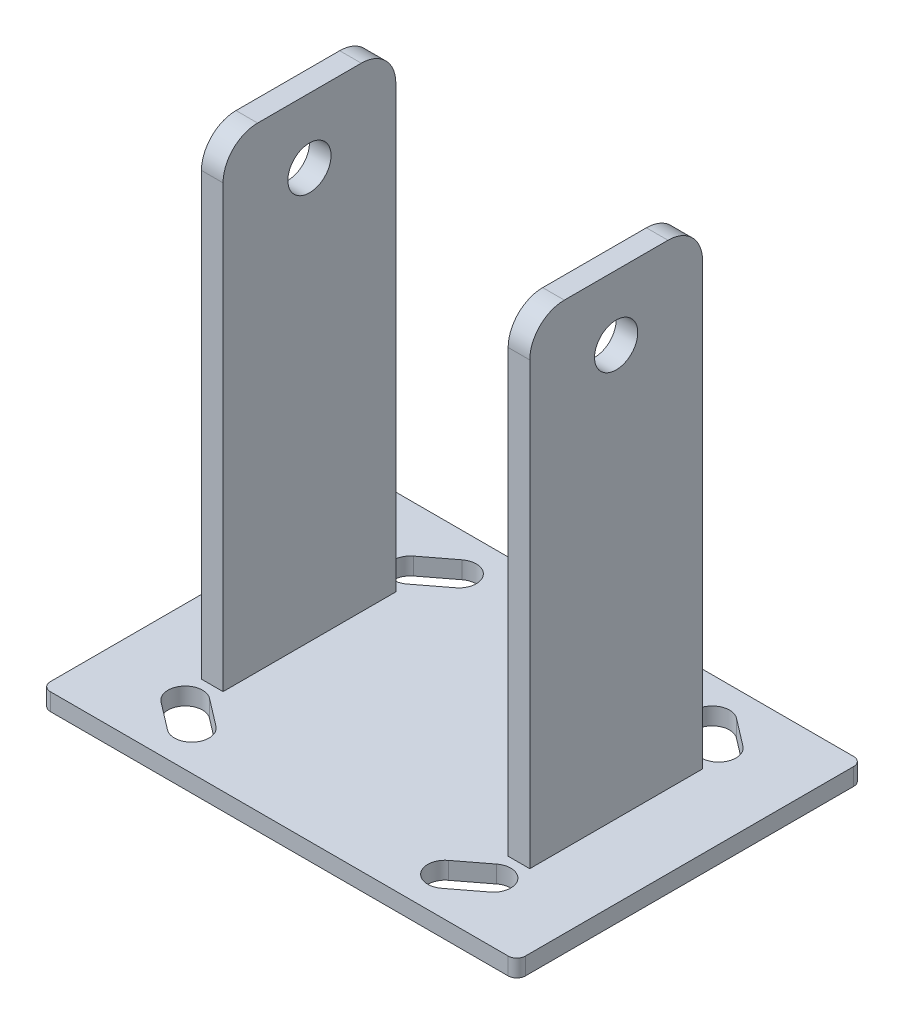
SolidWorks part; units mm, degrees
ref_plane "Front Plane" through (0, 0, 0) normal (0, 0, 1) x (1, 0, 0)
ref_plane "Top Plane" through (0, 0, 0) normal (0, 1, 0) x (1, 0, 0)
ref_plane "Right Plane" through (0, 0, 0) normal (1, 0, 0) x (0, 0, -1)
sketch "Sketch1" plane through (0, 0, 0) normal (0, 1, 0) x (1, 0, 0)
  line L0 (-69.85, 0) -> (69.85, 0) construction
  line L1 (69.85, 50.8) -> (-69.85, 50.8)
  line L2 (69.85, 50.8) -> (69.85, -50.8)
  line L3 (69.85, -50.8) -> (-69.85, -50.8)
  line L4 (-69.85, 50.8) -> (-69.85, -50.8)
  line L5 (69.85, 50.8) -> (-69.85, -50.8) construction
  line L6 (69.85, -50.8) -> (-69.85, 50.8) construction
  line L7 (0, 50.8) -> (0, -50.8) construction
  line L8 (-52.07, 50.8) -> (-52.07, -50.8) construction
  line L9 (52.07, 50.8) -> (52.07, -50.8) construction
  line L10 (-30.48, 50.8) -> (-30.48, -50.8) construction
  line L11 (30.48, 50.8) -> (30.48, -50.8) construction
  line L12 (-69.85, 27.94) -> (69.85, 27.94) construction
  line L13 (-69.85, 44.45) -> (69.85, 44.45) construction
  line L14 (-52.07, 27.94) -> (-30.48, 44.45) construction
  line L15 (-52.07, 44.45) -> (-30.48, 27.94) construction
  line L16 (-33.2043, 42.3667) -> (-49.3457, 30.0233) construction
  line L17 (-46.2598, 25.988) -> (-30.1185, 38.3314) construction
  line L18 (-46.2598, 25.988) -> (-52.4315, 34.0586) construction
  line L19 (-30.1185, 38.3314) -> (-36.2902, 46.402) construction
  line L20 (-52.4315, 34.0586) -> (-36.2902, 46.402) construction
  line L21 (-46.2598, 25.988) -> (-36.2902, 46.402) construction
  line L22 (-30.1185, 38.3314) -> (-52.4315, 34.0586) construction
  line L23 (-40.3255, 43.3162) -> (-34.1538, 35.2455) construction
  line L24 (-48.3962, 37.1445) -> (-42.2245, 29.0738) construction
  line L25 (-48.3962, 37.1445) -> (-40.3255, 43.3162)
  line L26 (-34.1538, 35.2455) -> (-42.2245, 29.0738)
  line L27 (34.1538, 35.2455) -> (42.2245, 29.0738)
  line L28 (48.3962, 37.1445) -> (40.3255, 43.3162)
  line L29 (34.1538, -35.2455) -> (42.2245, -29.0738)
  line L30 (48.3962, -37.1445) -> (40.3255, -43.3162)
  line L31 (-48.3962, -37.1445) -> (-40.3255, -43.3162)
  line L32 (-34.1538, -35.2455) -> (-42.2245, -29.0738)
  arc A0 (-40.3255, 43.3162) -> (-34.1538, 35.2455) centre (-37.2397, 39.2808) cw
  arc A1 (-48.3962, 37.1445) -> (-42.2245, 29.0738) centre (-45.3103, 33.1092) ccw
  arc A2 (48.3962, 37.1445) -> (42.2245, 29.0738) centre (45.3103, 33.1092) cw
  arc A3 (40.3255, 43.3162) -> (34.1538, 35.2455) centre (37.2397, 39.2808) ccw
  arc A4 (48.3962, -37.1445) -> (42.2245, -29.0738) centre (45.3103, -33.1092) ccw
  arc A5 (40.3255, -43.3162) -> (34.1538, -35.2455) centre (37.2397, -39.2808) cw
  arc A6 (-48.3962, -37.1445) -> (-42.2245, -29.0738) centre (-45.3103, -33.1092) cw
  arc A7 (-40.3255, -43.3162) -> (-34.1538, -35.2455) centre (-37.2397, -39.2808) ccw
  point P0 (0, 0)
  point P26 (-41.275, 36.195)
  point P30 (-41.275, 36.195)
  dimension "D1" = 101.6
  dimension "D2" = 139.7
  dimension "D3" = 17.78
  dimension "D4" = 17.78
  dimension "D5" = 39.37
  dimension "D6" = 22.86
  dimension "D7" = 6.35
  dimension "D8" = 20.32
  dimension "D9" = 10.16
  dimension "D10" = 5.08
  dimension "D11" = 5.08
extrude "Boss-Extrude1" add sketch "Sketch1" along normal blind 5.08 contours L1 L4 L3 L2 A7 L31 A6 L32 A1 L25 A0 L26 A3 L28 A2 L27 L30 A5 L29 A4
fillet "Fillet1" radius 2.54 4 edges at (-69.85, 2.54, 50.8) (69.85, 2.54, 50.8) (69.85, 2.54, -50.8) (-69.85, 2.54, -50.8)
sketch "Sketch2" plane through (0, 5.08, 0) normal (0, 1, 0) x (1, 0, 0)
  line L0 (-41.91, 50.8) -> (-41.91, -50.8) construction
  line L1 (67.31, 50.8) -> (-67.31, 50.8) construction
  line L2 (67.31, -50.8) -> (-67.31, -50.8) construction
  line L3 (48.26, -25.4) -> (41.91, -25.4)
  line L4 (0, 50.8) -> (0, -50.8) construction
  line L5 (-69.85, 0) -> (69.85, 0) construction
  line L6 (-69.85, 48.26) -> (-69.85, -48.26) construction
  line L7 (69.85, 48.26) -> (69.85, -48.26) construction
  line L8 (48.26, 25.4) -> (41.91, -25.4) construction
  line L9 (-48.26, -25.4) -> (-41.91, -25.4)
  line L10 (-48.26, -25.4) -> (-48.26, 25.4)
  line L11 (-48.26, 25.4) -> (-41.91, 25.4)
  line L12 (-41.91, -25.4) -> (-41.91, 25.4)
  line L13 (-48.26, -25.4) -> (-41.91, 25.4) construction
  line L14 (-48.26, 25.4) -> (-41.91, -25.4) construction
  line L15 (48.26, -25.4) -> (41.91, 25.4) construction
  line L16 (41.91, -25.4) -> (41.91, 25.4)
  line L17 (48.26, 25.4) -> (41.91, 25.4)
  line L18 (48.26, -25.4) -> (48.26, 25.4)
  point P16 (-45.085, 0)
  dimension "D2" = 41.91
  dimension "D3" = 50.8
  dimension "D4" = 6.35
extrude "Boss-Extrude2" add sketch "Sketch2" along normal blind 139.7
fillet "Fillet2" radius 10.16 4 edges at (-45.085, 144.78, 25.4) (45.085, 144.78, 25.4) (45.085, 144.78, -25.4) (-45.085, 144.78, -25.4)
sketch "Sketch3" plane through (-48.26, 0, 0) normal (-1, 0, 0) x (0, 0, 1)
  line L0 (-15.24, 144.78) -> (15.24, 144.78) construction
  line L1 (-25.4, 134.62) -> (-25.4, 5.08) construction
  circle A0 centre (0, 125.73) radius 6.35
  dimension "D3" = 12.7
  dimension "D1" = 19.05
  dimension "D2" = 25.4
extrude "Cut-Extrude1" cut sketch "Sketch3" against normal through all
